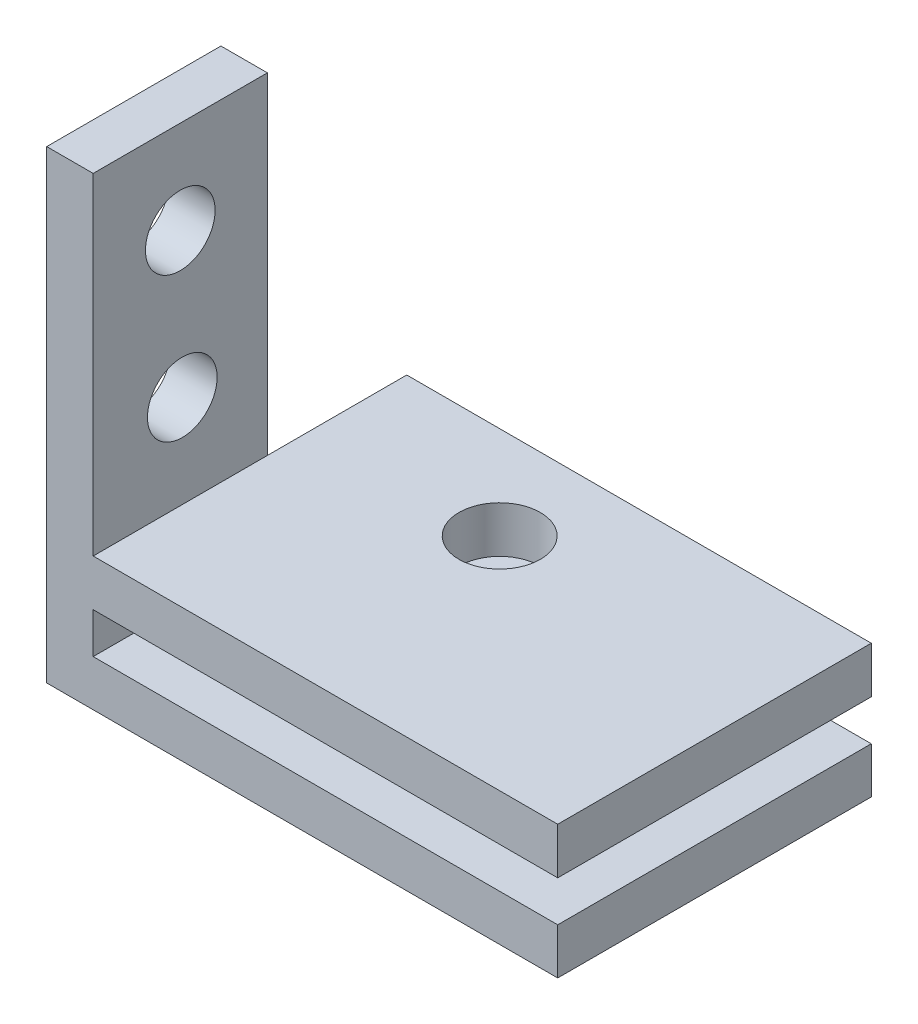
SolidWorks part; units mm, degrees
ref_plane "Front Plane" through (0, 0, 0) normal (0, 0, 1) x (1, 0, 0)
ref_plane "Top Plane" through (0, 0, 0) normal (0, 1, 0) x (1, 0, 0)
ref_plane "Right Plane" through (0, 0, 0) normal (1, 0, 0) x (0, 0, -1)
sketch "Sketch1" plane through (0, 0, 0) normal (1, 0, 0) x (0, 0, -1)
  line L1 (-0.7404, 9.0244) -> (6.7596, 9.0244)
  line L2 (-0.7404, 9.0244) -> (-0.7404, -10.9756)
  line L3 (-0.7404, -10.9756) -> (6.7596, -10.9756)
  line L4 (6.7596, 9.0244) -> (6.7596, -10.9756)
  dimension "D1" = 20
  dimension "D2" = 7.5
extrude "Boss-Extrude2" add sketch "Sketch1" along normal blind 2
sketch "Sketch2" plane through (2, 0, 0) normal (1, 0, 0) x (0, 0, -1)
  line L0 (-0.7404, 9.0244) -> (-0.7404, -10.9756) construction
  line L1 (6.7596, -10.9756) -> (-0.7404, -10.9756)
  line L2 (6.7596, -10.9756) -> (6.7596, -8.9921)
  line L3 (6.7596, -8.9921) -> (-0.7404, -8.9921)
  line L4 (-0.7404, -10.9756) -> (-0.7404, -8.9921)
extrude "Boss-Extrude3" add sketch "Sketch2" along normal blind 20
sketch "Sketch3" plane through (2, 0, 0) normal (1, 0, 0) x (0, 0, -1)
  line L0 (6.7596, -8.9921) -> (6.7596, 9.0244) construction
  line L1 (-0.7404, -8.9921) -> (6.7596, -8.9921)
  line L2 (-0.7404, -8.9921) -> (-0.7404, -7.2421)
  line L3 (-0.7404, -7.2421) -> (6.7596, -7.2421)
  line L4 (6.7596, -8.9921) -> (6.7596, -7.2421)
  line L6 (-0.7404, -7.2421) -> (6.7596, -7.2421)
  line L7 (-0.7404, -7.2421) -> (-0.7404, -5.2421)
  line L8 (-0.7404, -5.2421) -> (6.7596, -5.2421)
  line L9 (6.7596, -7.2421) -> (6.7596, -5.2421)
  line M5 (6.7596, -8.9921) -> (6.7596, 9.0244)
  line M7 (-0.7404, 9.0244) -> (-0.7404, -8.9921)
  dimension "D1" = 2
  dimension "D2" = 1.75
extrude "Boss-Extrude4" add sketch "Sketch3" along normal blind 20 contours L8 L3 M7 M5
sketch "Sketch5" plane through (2, 0, 0) normal (1, 0, 0) x (0, 0, -1)
  line L0 (6.7596, -5.2421) -> (6.7596, 9.0244) construction
  line L2 (6.7596, 9.0244) -> (-0.7404, 9.0244) construction
  line L5 (-0.7404, -5.2421) -> (6.7596, -5.2421) construction
  circle A0 centre (3.0096, 5.0244) radius 1.5
  circle A1 centre (3.0965, -1.2421) radius 1.5
  dimension "D1" = 3.75
  dimension "D2" = 4
  dimension "D3" = 4
extrude "Cut-Extrude1" cut sketch "Sketch5" against normal blind 20
sketch "Sketch6" plane through (0, 0, -6.7596) normal (0, 0, -1) x (-1, 0, 0)
  line L0 (-2, -5.2421) -> (-2, -7.2421)
  line L1 (-2, -7.2421) -> (-2, -10.9756)
  line L2 (-22, -10.9756) -> (0, -10.9756) construction
sketch "Sketch7" plane through (0, 0, -6.7596) normal (0, 0, -1) x (-1, 0, 0)
  line L1 (-22, -5.2421) -> (-2, -5.2421)
  line L2 (-22, -5.2421) -> (-22, -7.2421)
  line L3 (-22, -7.2421) -> (-2, -7.2421)
  line L4 (-2, -5.2421) -> (-2, -7.2421)
extrude "Boss-Extrude6" add sketch "Sketch7" along normal blind 6
sketch "Sketch8" plane through (0, 0, -6.7596) normal (0, 0, -1) x (-1, 0, 0)
  line L1 (-22, -8.9921) -> (-2, -8.9921)
  line L2 (-22, -8.9921) -> (-22, -10.9756)
  line L3 (-22, -10.9756) -> (-2, -10.9756)
  line L4 (-2, -8.9921) -> (-2, -10.9756)
extrude "Boss-Extrude7" add sketch "Sketch8" along normal blind 6
sketch "Sketch9" plane through (0, -5.2421, 0) normal (0, 1, 0) x (1, 0, 0)
  line L0 (2, -0.7404) -> (2, 6.7596) construction
  line L1 (22, -0.7404) -> (2, -0.7404) construction
  circle A0 centre (10, 8.7596) radius 1.75
  dimension "D1" = 8
  dimension "D2" = 9.5
extrude "Cut-Extrude2" cut sketch "Sketch9" against normal blind 6
